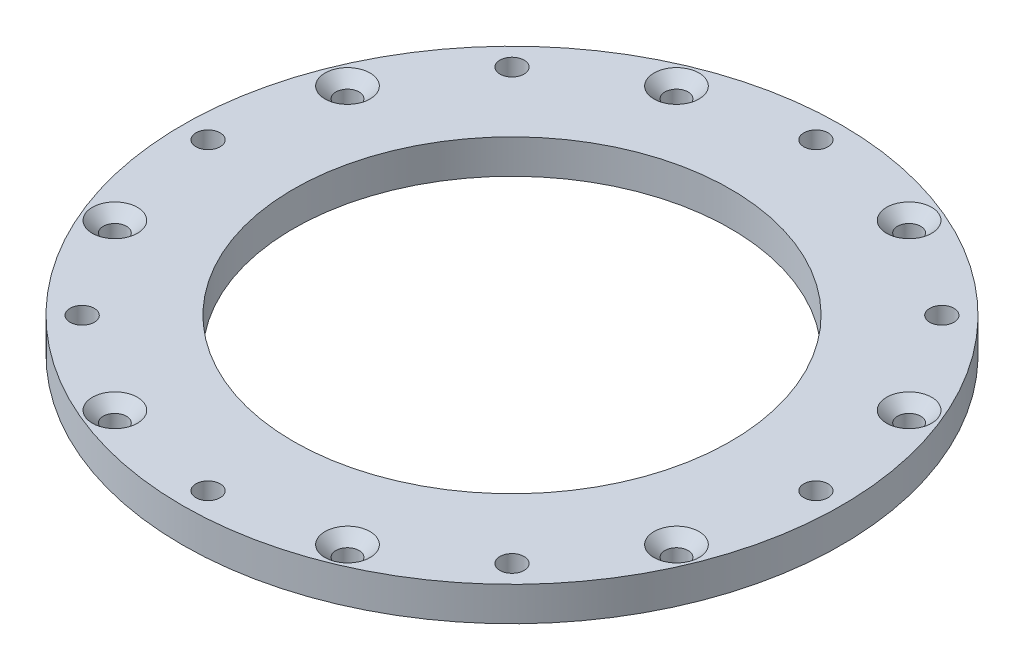
SolidWorks part; units mm, degrees
material "Thornel Mat VMA"
ref_plane "前视基准面" through (0, 0, 0) normal (0, 0, 1) x (1, 0, 0)
ref_plane "上视基准面" through (0, 0, 0) normal (0, 1, 0) x (1, 0, 0)
ref_plane "右视基准面" through (0, 0, 0) normal (1, 0, 0) x (0, 0, -1)
other "Configuration Table"
sketch "草图1" plane through (0, 0, 0) normal (0, 1, 0) x (1, 0, 0)
  line L1 (-105, -26.125) -> (105, -26.125)
  line L2 (-105, -26.125) -> (-105, 26.125)
  line L3 (-105, 26.125) -> (105, 26.125)
  line L4 (105, -26.125) -> (105, 26.125)
  line L5 (-105, -26.125) -> (105, 26.125) construction
  line L6 (-105, 26.125) -> (105, -26.125) construction
  circle A0 centre (-105, 0) radius 26.125
  point P0 (0, 0)
  dimension "D1" = 52.25
  dimension "D2" = 210
extrude "凸台-拉伸1" add sketch "草图1" along normal blind 5 contours A0 L1 L4 L3 | L2 A0 | L2 A0
sketch "草图2" plane through (0, 5, 0) normal (0, 1, 0) x (1, 0, 0)
  circle A0 centre (-105, 0) radius 13.5 construction
  circle A1 centre (-91.5, 0) radius 1.525
  circle A2 centre (-98.25, -11.6913) radius 1.525
  circle A3 centre (-111.75, -11.6913) radius 1.525
  circle A4 centre (-118.5, 0) radius 1.525
  circle A5 centre (-111.75, 11.6913) radius 1.525
  circle A6 centre (-98.25, 11.6913) radius 1.525
  point P17 (-105, 0)
  dimension "D1" = 27
  dimension "D2" = 3.05
  dimension "D3" = 6
extrude "切除-拉伸1" cut sketch "草图2" against normal through all
sketch "草图3" plane through (0, 5, 0) normal (0, 1, 0) x (1, 0, 0)
  line L0 (105, -26.125) -> (105, 26.125) construction
  circle A0 centre (105, 0) radius 48.25
  dimension "D1" = 96.5
extrude "凸台-拉伸2" add sketch "草图3" against normal up to surface (5 mm away) up to face at (-91.5, 0, 1.525)
sketch "草图4" plane through (0, 5, 0) normal (0, 1, 0) x (1, 0, 0)
  circle A0 centre (105, 0) radius 32
  dimension "D1" = 64
extrude "切除-拉伸2" cut sketch "草图4" against normal through all
sketch "草图5" plane through (0, 5, 0) normal (0, 1, 0) x (1, 0, 0)
  circle A0 centre (105, 0) radius 25 construction
  circle A2 centre (130, 0) radius 1.525
  circle A3 centre (117.5, -21.6506) radius 1.525
  circle A4 centre (92.5, -21.6506) radius 1.525
  circle A5 centre (80, 0) radius 1.525
  circle A6 centre (92.5, 21.6506) radius 1.525
  circle A7 centre (117.5, 21.6506) radius 1.525
  point P25 (105, 0)
  dimension "D1" = 50
  dimension "D2" = 3.05
  dimension "D3" = 6
fillet "圆角1" radius 40 2 edges at (64.4347, 2.5, -26.125) (64.4347, 2.5, 26.125)
sketch "草图9" plane through (0, 5, 0) normal (0, 1, 0) x (1, 0, 0)
  circle A0 centre (-105, 0) radius 7.5
  dimension "D1" = 15
extrude "切除-拉伸7" cut sketch "草图9" against normal through all
sketch "草图10" plane through (0, 5, 0) normal (0, 1, 0) x (1, 0, 0)
  circle A0 centre (105, 0) radius 44.5 construction
  circle A1 centre (149.5, 0) radius 1.775
  circle A2 centre (136.4663, -31.4663) radius 1.775
  circle A3 centre (105, -44.5) radius 1.775
  circle A4 centre (73.5337, -31.4663) radius 1.775
  circle A5 centre (60.5, 0) radius 1.775
  circle A6 centre (73.5337, 31.4663) radius 1.775
  circle A7 centre (105, 44.5) radius 1.775
  circle A8 centre (136.4663, 31.4663) radius 1.775
  point P21 (105, 0)
  dimension "D1" = 89
  dimension "D2" = 3.55
  dimension "D3" = 8
sketch "草图15" plane through (0, 5, 0) normal (0, 1, 0) x (1, 0, 0)
  line L0 (-105, 0) -> (-123.6195, 10.75) construction
  line L1 (-105, 0) -> (-105, 26.125) construction
  circle A0 centre (-105, 0) radius 21.5 construction
  circle A1 centre (-123.6195, 10.75) radius 1.525
  circle A2 centre (-105, 21.5) radius 1.525
  circle A3 centre (-86.3805, 10.75) radius 1.525
  circle A4 centre (-86.3805, -10.75) radius 1.525
  circle A5 centre (-105, -21.5) radius 1.525
  circle A6 centre (-123.6195, -10.75) radius 1.525
  point P19 (-105, 0)
  dimension "D1" = 43
  dimension "D2" = 3.05
  dimension "D3" = 60
  dimension "D4" = 6
extrude "切除-拉伸10" cut sketch "草图15" against normal through all
sketch "草图16" plane through (0, 5, 0) normal (0, 1, 0) x (1, 0, 0)
  circle A0 centre (-118.5, 0) radius 1.525 construction
  circle A1 centre (-111.75, -11.6913) radius 1.525 construction
  circle A2 centre (-98.25, -11.6913) radius 1.525 construction
  circle A3 centre (-91.5, 0) radius 1.525 construction
  circle A4 centre (-98.25, 11.6913) radius 1.525 construction
  circle A5 centre (-111.75, 11.6913) radius 1.525 construction
  circle A6 centre (-118.5, 0) radius 1.525 construction
  circle A7 centre (-111.75, -11.6913) radius 1.525 construction
  circle A8 centre (-98.25, -11.6913) radius 1.525 construction
  circle A9 centre (-91.5, 0) radius 1.525 construction
  circle A10 centre (-98.25, 11.6913) radius 1.525 construction
  circle A11 centre (-111.75, 11.6913) radius 1.525 construction
  circle A12 centre (-118.5, 0) radius 3.525
  circle A13 centre (-111.75, -11.6913) radius 3.525
  circle A14 centre (-98.25, -11.6913) radius 3.525
  circle A15 centre (-91.5, 0) radius 3.525
  circle A16 centre (-98.25, 11.6913) radius 3.525
  circle A17 centre (-111.75, 11.6913) radius 3.525
  circle A18 centre (-118.5, 0) radius 0.525 construction
  circle A19 centre (-111.75, -11.6913) radius 0.525 construction
  circle A20 centre (-98.25, -11.6913) radius 0.525 construction
  circle A21 centre (-91.5, 0) radius 0.525 construction
  circle A22 centre (-98.25, 11.6913) radius 0.525 construction
  circle A23 centre (-111.75, 11.6913) radius 0.525 construction
  dimension "D1" = 2
  dimension "D2" = 1
extrude "切除-拉伸11" cut sketch "草图16" against normal through all
sketch "草图17" plane through (0, 5, 0) normal (0, 1, 0) x (1, 0, 0)
  line L2 (-105, -26.125) -> (46.5573, -26.125)
  line L3 (46.5573, 26.125) -> (-105, 26.125)
  line L4 (-105, -26.125) -> (46.5573, -26.125)
  line L5 (46.5573, 26.125) -> (-105, 26.125)
  circle A0 centre (105, 0) radius 48.25
  arc A5 (73.0469, -36.1533) -> (46.5573, -26.125) centre (46.5573, -66.125) ccw
  arc A6 (73.0469, -36.1533) -> (73.0469, 36.1533) centre (105, 0) ccw
  arc A7 (46.5573, 26.125) -> (73.0469, 36.1533) centre (46.5573, 66.125) ccw
  arc A8 (-105, 26.125) -> (-105, -26.125) centre (-105, 0) ccw
  arc A9 (73.0469, -36.1533) -> (46.5573, -26.125) centre (46.5573, -66.125) ccw
  arc A10 (73.0469, -36.1533) -> (73.0469, 36.1533) centre (105, 0) ccw
  arc A11 (46.5573, 26.125) -> (73.0469, 36.1533) centre (46.5573, 66.125) ccw
  arc A12 (-105, 26.125) -> (-105, -26.125) centre (-105, 0) ccw
  circle M8 centre (-98.25, 11.6913) radius 3.525
  circle M9 centre (-91.5, 0) radius 3.525
  circle M10 centre (-98.25, -11.6913) radius 3.525
  circle M11 centre (-111.75, -11.6913) radius 3.525
  circle M12 centre (-118.5, 0) radius 3.525
  circle M13 centre (-111.75, 11.6913) radius 3.525
  circle M14 centre (-123.6195, -10.75) radius 1.525
  circle M15 centre (-105, -21.5) radius 1.525
  circle M16 centre (-86.3805, -10.75) radius 1.525
  circle M17 centre (-86.3805, 10.75) radius 1.525
  circle M18 centre (-105, 21.5) radius 1.525
  circle M19 centre (-123.6195, 10.75) radius 1.525
  circle M36 centre (-105, 0) radius 7.5
  line M38 (-105, -26.125) -> (46.5573, -26.125)
  arc M39 (46.5573, -26.125) -> (73.0469, -36.1533) centre (46.5573, -66.125) cw
  arc M41 (73.0469, 36.1533) -> (46.5573, 26.125) centre (46.5573, 66.125) cw
  line M42 (46.5573, 26.125) -> (-105, 26.125)
  arc M43 (-105, 26.125) -> (-105, -26.125) centre (-105, 0) ccw
  dimension "D1" = 96.5
  dimension "D2" = 0
extrude "切除-拉伸12" cut sketch "草图17" against normal through all contours A0 M41 M42 M43 M38 M39 M9 M11 M13 M15 M17 M19 M36 M18 M16 M14 M12 M10 M8
extrude "切除-拉伸13" cut sketch "草图10" against normal through all contours A6 | A7 | A8 | A2 | A4 | A5 | A1 | A3
sketch "草图19" plane through (0, 5, 0) normal (0, 1, 0) x (1, 0, 0)
  line L0 (122.0294, 41.1126) -> (105, 0) construction
  line L1 (105, 44.5) -> (105, 0) construction
  circle A0 centre (105, 0) radius 44.5 construction
  circle A2 centre (122.0294, 41.1126) radius 1.525
  circle A3 centre (146.1126, 17.0294) radius 1.525
  circle A4 centre (146.1126, -17.0294) radius 1.525
  circle A5 centre (122.0294, -41.1126) radius 1.525
  circle A6 centre (87.9706, -41.1126) radius 1.525
  circle A7 centre (63.8874, -17.0294) radius 1.525
  circle A8 centre (63.8874, 17.0294) radius 1.525
  circle A9 centre (87.9706, 41.1126) radius 1.525
  point P25 (105, 0)
  dimension "D1" = 89
  dimension "D3" = 3.05
  dimension "D2" = 22.5
  dimension "D4" = 8
extrude "切除-拉伸14" cut sketch "草图19" against normal through all
sketch "草图26" plane through (0, 5, 0) normal (0, 1, 0) x (1, 0, 0)
  point P0 (87.9706, 41.1126)
  point P3 (122.0294, 41.1126)
  point P6 (146.1126, 17.0294)
  point P9 (146.1126, -17.0294)
  point P12 (122.0294, -41.1126)
  point P15 (87.9706, -41.1126)
  point P18 (63.8874, -17.0294)
  point P21 (63.8874, 17.0294)
hole_wizard "M3 开槽沉头木螺钉的锥形沉头孔2" positions "草图26" profile "草图27" countersink size "M3" standard "GB" end condition through all
sketch "草图27" plane through (87.9706, 5, -41.1126) normal (1, 0, 0) x (0, 0, 1)
  line L0 (0, 0) -> (0, 5)
  line L1 (0, 5) -> (1.7, 5)
  line L2 (1.7, 5) -> (1.7, 1.6)
  line L3 (1.7, 1.6) -> (3.3, 0)
  line L5 (3.3, 0) -> (0, 0)
  line L6 (-1.7, 1.6) -> (-3.3, 0) construction
  line L11 (0, -6.35) -> (0, 107.95) construction
  dimension "通孔孔直径" = 3.4
  dimension "通孔孔深度" = 5
  dimension "近端锥形沉头孔直径" = 6.6
  dimension "近端锥形沉头孔角度" = 90
sketch "草图28" plane through (0, 5, 0) normal (0, 1, 0) x (1, 0, 0)
  circle A0 centre (105, 0) radius 42.5 construction
  circle A1 centre (147.5, 0) radius 1.75
  circle A2 centre (62.5, 0) radius 1.775
  dimension "D1" = 85
  dimension "D2" = 3.55
  dimension "D3" = 3.5
